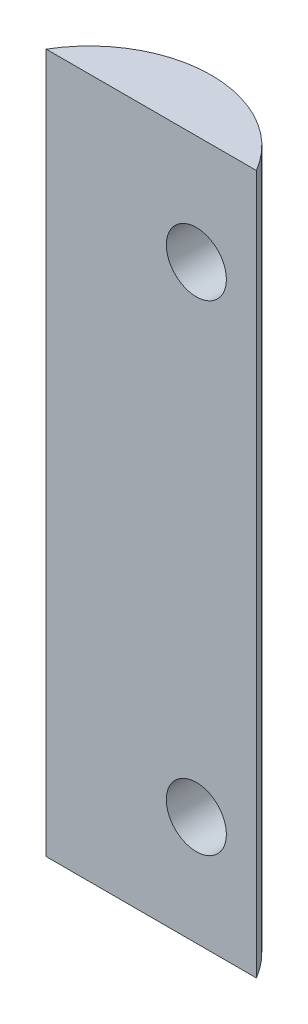
SolidWorks part; units mm, degrees
ref_plane "Front Plane" through (0, 0, 0) normal (0, 0, 1) x (1, 0, 0)
ref_plane "Top Plane" through (0, 0, 0) normal (0, 1, 0) x (1, 0, 0)
ref_plane "Right Plane" through (0, 0, 0) normal (1, 0, 0) x (0, 0, -1)
sketch "Sketch2" plane through (0, 0, 0) normal (0, 1, 0) x (1, 0, 0)
  line L2 (0, 0) -> (6.35, 0)
  line L3 (0, 0) -> (-15.875, 0)
  arc A2 (-15.875, 0) -> (6.35, 0) centre (-4.7625, -6.5484) cw
  point P4 (0, 0)
  point P7 (-4.7625, 6.35)
  dimension "D1" = 6.35
  dimension "D2" = 15.875
  dimension "D3" = 6.35
extrude "Boss-Extrude1" add sketch "Sketch2" along normal blind 73.93 from offset 6.35 offset against normal yes
sketch "Sketch1" plane through (0, 0, 0) normal (0, 0, 1) x (1, 0, 0)
  line L0 (0, -6.35) -> (0, 67.58) construction
  line L1 (-15.875, -6.35) -> (6.35, -6.35) construction
  line L2 (-15.875, 67.58) -> (6.35, 67.58) construction
  circle A1 centre (0, 56.0151) radius 3.175
  circle A2 centre (0, 5.2149) radius 3.175
  point P12 (0, 7.9259)
  point P13 (0, 27.2405)
  dimension "D1" = 6.35
  dimension "D3" = 11.5649
  dimension "D2" = 11.5649
extrude "Cut-Extrude2" cut sketch "Sketch1" against normal through all both
